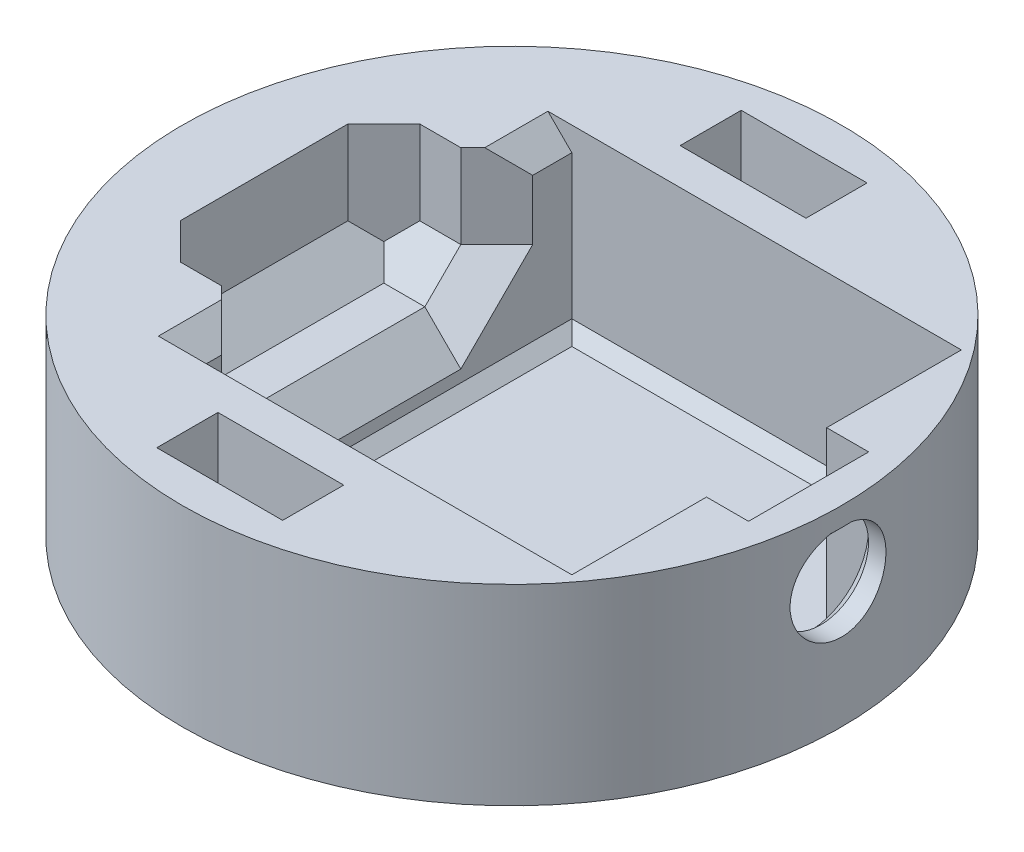
SolidWorks part; units mm, degrees
ref_plane "Front Plane" through (0, 0, 0) normal (0, 0, 1) x (1, 0, 0)
ref_plane "Top Plane" through (0, 0, 0) normal (0, 1, 0) x (1, 0, 0)
ref_plane "Right Plane" through (0, 0, 0) normal (1, 0, 0) x (0, 0, -1)
sketch "Sketch1" plane through (0, 0, 0) normal (0, 1, 0) x (1, 0, 0)
  circle A0 centre (0, 0) radius 27.5
  dimension "D1" = 55
extrude "Boss-Extrude1" add sketch "Sketch1" along normal blind 16
sketch "Sketch3" plane through (0, 16, 0) normal (0, 1, 0) x (1, 0, 0)
  line L0 (21.25, 0) -> (27.5, 0) construction
  line L1 (-11.25, -16.25) -> (16.25, -16.25)
  line L2 (-16.25, -16.25) -> (-16.25, 16.25) construction
  line L3 (-11.25, 16.25) -> (16.25, 16.25) construction
  line L4 (16.25, -16.25) -> (16.25, -1.9281) construction
  line L5 (-11.25, -11.25) -> (0, 0) construction
  line L6 (-11.25, 11.25) -> (0, 0) construction
  line L7 (0, 0) -> (16.25, 0) construction
  line L8 (21.25, 0) -> (27.5, 0) construction
  line L9 (-16.25, 16.25) -> (-11.25, 16.25) construction
  line L10 (16.25, 16.25) -> (21.25, 16.25)
  line L11 (16.25, 0) -> (16.25, -16.25) construction
  line L12 (16.25, -16.25) -> (21.25, -16.25)
  line L13 (21.25, 16.25) -> (21.25, -16.25)
  line L14 (-16.25, 16.25) -> (-11.25, 16.25) construction
  line L15 (-16.25, 16.25) -> (-16.25, -16.25) construction
  line L16 (-16.25, -16.25) -> (-11.25, -16.25) construction
  line L17 (-11.25, 16.25) -> (-11.25, -16.25)
  line L18 (-16.25, 16.25) -> (-11.25, 16.25) construction
  line L19 (-16.25, 16.25) -> (-11.25, 11.25) construction
  line L20 (-16.25, -16.25) -> (-11.25, -11.25) construction
  line L21 (-16.25, -16.25) -> (-11.25, -16.25) construction
  line L22 (0, 0) -> (16.25, 0) construction
  line L23 (16.25, 6.8206) -> (16.25, 16.25) construction
  line L24 (16.25, 16.25) -> (16.25, 0) construction
  line L25 (16.25, 0) -> (21.25, 0) construction
  line L26 (16.25, 0) -> (21.25, 0) construction
  line L27 (0, 0) -> (16.25, 16.25) construction
  line L28 (0, 0) -> (16.25, -16.25) construction
  line L29 (-11.25, 16.25) -> (16.25, 16.25)
  circle A0 centre (0, 0) radius 27.5 construction
  point P1 (0, 0)
  dimension "D1" = 32.5
  dimension "D2" = 32.5
  dimension "D3" = 27.5
  dimension "D5" = 5
  dimension "D6" = 5
extrude "Cut-Extrude1" cut sketch "Sketch3" against normal blind 15
sketch "Sketch4" plane through (21.25, 0, 0) normal (-1, 0, 0) x (0, 0, 1)
  line L0 (0, 6.5) -> (0, 10.5) construction
  line L1 (16.25, 1) -> (-16.25, 1) construction
  line L2 (0, 1) -> (0, 6.5) construction
  line L3 (-2.1032, 13.9024) -> (2.1032, 13.9024)
  arc A0 (-2.1032, 13.9024) -> (2.1032, 13.9024) centre (0, 10.5) ccw
  arc A1 (2.1032, 13.9024) -> (-2.1032, 13.9024) centre (0, 10.5) ccw construction
  dimension "D2" = 8
  dimension "D1" = 9.5
extrude "Cut-Extrude2" cut sketch "Sketch4" against normal blind 15
sketch "Sketch6" plane through (0, 16, 0) normal (0, 1, 0) x (1, 0, 0)
  line L0 (-11.25, 16.25) -> (-11.25, -16.25) construction
  line L1 (-20.6746, 9.9839) -> (-1.8254, 9.9839)
  line L2 (-20.6746, 9.9839) -> (-20.6746, -9.9839)
  line L3 (-20.6746, -9.9839) -> (-1.8254, -9.9839)
  line L4 (-1.8254, 9.9839) -> (-1.8254, -9.9839)
  line L5 (-20.6746, 9.9839) -> (-1.8254, -9.9839) construction
  line L6 (-20.6746, -9.9839) -> (-1.8254, 9.9839) construction
  point P0 (-11.25, 0)
extrude "Cut-Extrude4" cut sketch "Sketch6" against normal blind 10
chamfer "Chamfer2" distance 3 angle 45 6 edges at (-15.9623, 6, 9.9839) (-20.6746, 6, 0) (-15.9623, 6, -9.9839) (-11.25, 11, 9.9839) (-11.25, 11, -9.9839) (-11.25, 6, 0)
chamfer "Chamfer3" distance 3 angle 45 2 edges at (-20.6746, 12.5, -9.9839) (-20.6746, 12.5, 9.9839)
sketch "Sketch8" plane through (0, 16, 0) normal (0, 1, 0) x (1, 0, 0)
  line L0 (21.25, -16.25) -> (21.25, 16.25) construction
  line L1 (17.7452, -5.0134) -> (24.7548, -5.0134)
  line L2 (17.7452, -5.0134) -> (17.7452, 5.0134)
  line L3 (17.7452, 5.0134) -> (24.7548, 5.0134)
  line L4 (24.7548, -5.0134) -> (24.7548, 5.0134)
  line L5 (17.7452, -5.0134) -> (24.7548, 5.0134) construction
  line L6 (17.7452, 5.0134) -> (24.7548, -5.0134) construction
  point P0 (21.25, 0)
extrude "Cut-Extrude5" cut sketch "Sketch8" against normal up to surface (15 mm away) up to face at (5, 1, 0)
chamfer "Chamfer4" distance 1 angle 45 2 edges at (24.7548, 6.5, 0) (24.7548, 13.9024, 0)
chamfer "Chamfer5" distance 2 angle 45 1 edges at (24.7548, 1, 0)
chamfer "Chamfer6" distance 2 angle 45 2 edges at (-11.25, 16, 14.6169) (-11.25, 16, -14.6169)
chamfer "Chamfer7" distance 1 angle 45 7 edges at (22.0024, 1, -5.0134) (22.0024, 1, 5.0134) (21.25, 1, -10.6317) (5, 1, -16.25) (-11.25, 1, 0) (5, 1, 16.25) (21.25, 1, 10.6317)
chamfer "Chamfer8" distance 0.5 angle 45 1 edges at (27.5, 13.9024, 0)
sketch "Sketch9" plane through (0, 16, 0) normal (0, 1, 0) x (1, 0, 0)
  line L0 (0, 21.8334) -> (5.25, 24.3834) construction
  line L1 (-5.25, 19.2834) -> (5.25, 19.2834)
  line L2 (-5.25, 19.2834) -> (-5.25, 24.3834)
  line L3 (-5.25, 24.3834) -> (5.25, 24.3834)
  line L4 (5.25, 19.2834) -> (5.25, 24.3834)
  line L5 (-5.25, 19.2834) -> (0, 21.8334) construction
  line L6 (0, 21.8334) -> (5.25, 19.2834) construction
  line L7 (-5.25, -19.2834) -> (5.25, -19.2834)
  line L8 (-5.25, -19.2834) -> (-5.25, -24.3834)
  line L9 (-5.25, -24.3834) -> (5.25, -24.3834)
  line L10 (5.25, -19.2834) -> (5.25, -24.3834)
  line L11 (0, -21.8334) -> (5.25, -24.3834) construction
  line L12 (-5.25, -24.3834) -> (0, -21.8334) construction
  line L13 (-5.25, 24.3834) -> (0, 21.8334) construction
  line L14 (0, -21.8334) -> (5.25, -19.2834) construction
  line L15 (-5.25, -19.2834) -> (0, -21.8334) construction
  arc A0 (-5.25, -21.1928) -> (0, -21.8334) centre (0, 0) ccw construction
  arc A1 (-5.25, 21.1928) -> (-5.25, -21.1928) centre (0, 0) ccw construction
  arc A2 (5.25, -21.1928) -> (5.25, 21.1928) centre (0, 0) ccw construction
  arc A3 (0, 21.8334) -> (-5.25, 21.1928) centre (0, 0) ccw construction
  arc A4 (5.25, 21.1928) -> (0, 21.8334) centre (0, 0) ccw construction
  arc A5 (0, -21.8334) -> (5.25, -21.1928) centre (0, 0) ccw construction
  point P4 (0, 21.8334)
  point P9 (0, -21.8334)
  dimension "D1" = 10.5
  dimension "D2" = 5.1
  dimension "D3" = 10.5
  dimension "D4" = 5.1
extrude "Cut-Extrude6" cut sketch "Sketch9" against normal blind 5.5
